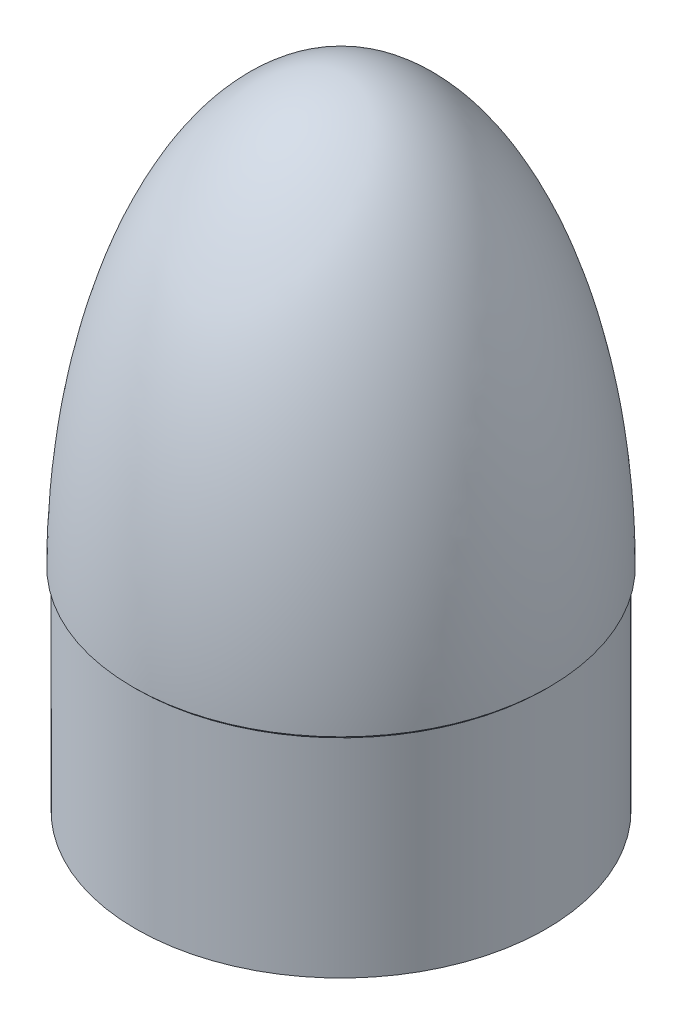
SolidWorks part; units mm, degrees
ref_plane "Front Plane" through (0, 0, 0) normal (0, 0, 1) x (1, 0, 0)
ref_plane "Top Plane" through (0, 0, 0) normal (0, 1, 0) x (1, 0, 0)
ref_plane "Right Plane" through (0, 0, 0) normal (1, 0, 0) x (0, 0, -1)
sketch "Sketch1" plane through (0, 0, 0) normal (0, 0, 1) x (1, 0, 0)
  line L3 (0, 0) -> (0, 202.3003) construction
  line L5 (0, 165.1) -> (0, 162.1)
  line L10 (76.975, 0) -> (76.975, -81.661)
  line L12 (76.975, -81.661) -> (79.375, -81.661)
  line L13 (79.375, -81.661) -> (79.375, -1.143)
  line L14 (80.518, 0) -> (79.375, -1.143)
  line L15 (79.375, -1.143) -> (80.518, -1.143) construction
  ellipse E0 centre (0, 0) end of major axis (0, 162.1) minor radius 76.975 (76.975, 0) -> (0, 162.1) ccw
  ellipse E1 centre (0, 0) end of major axis (0, -165.1) minor radius 80.518 (80.518, 0) -> (0, 165.1) ccw
  dimension "D1" = 158.75
  dimension "D2" = 80.518
  dimension "D3" = 165.1
  dimension "D4" = 161.036
  dimension "D5" = 2.4
  dimension "D6" = 3
  dimension "D7" = 45
revolve "Revolve1" add sketch "Sketch1" angle 360 about L5
